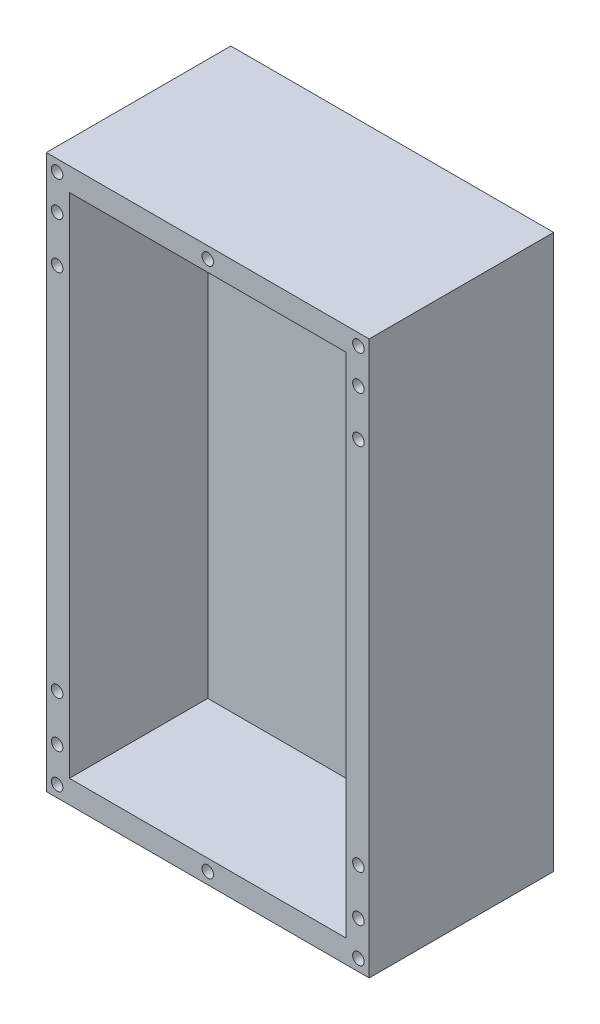
SolidWorks part; units mm, degrees
ref_plane "Front Plane" through (0, 0, 0) normal (0, 0, 1) x (1, 0, 0)
ref_plane "Top Plane" through (0, 0, 0) normal (0, 1, 0) x (1, 0, 0)
ref_plane "Right Plane" through (0, 0, 0) normal (1, 0, 0) x (0, 0, -1)
sketch "Sketch1" plane through (0, 0, 0) normal (0, 0, 1) x (1, 0, 0)
  line L0 (0, 609.6) -> (355.6, 0) construction
  line L1 (0, 609.6) -> (355.6, 609.6)
  line L2 (0, 609.6) -> (0, 0)
  line L3 (0, 0) -> (355.6, 0)
  line L4 (355.6, 609.6) -> (355.6, 0)
  line L5 (355.6, 609.6) -> (0, 0) construction
  line L9 (25.4, 584.2) -> (330.2, 584.2)
  line L10 (25.4, 584.2) -> (25.4, 25.4)
  line L11 (25.4, 25.4) -> (330.2, 25.4)
  line L12 (330.2, 584.2) -> (330.2, 25.4)
  line L13 (25.4, 584.2) -> (330.2, 25.4) construction
  line L14 (330.2, 584.2) -> (25.4, 25.4) construction
  point P12 (177.8, 304.8)
  point P13 (177.8, 304.8)
  dimension "D1" = 355.6
  dimension "D2" = 609.6
  dimension "D3" = 304.8
  dimension "D4" = 558.8
extrude "Boss-Extrude2" add sketch "Sketch1" along normal blind 203.2
ref_plane "Plane4" through (25.4, 584.2, 0) normal (0, -1, 0) x (-1, 0, 0)
sketch "Sketch4" plane through (0, 0, 0) normal (0, 0, -1) x (-1, 0, 0)
  line L1 (-330.2, 584.2) -> (-25.4, 584.2)
  line L2 (-330.2, 584.2) -> (-330.2, 25.4)
  line L3 (-330.2, 25.4) -> (-25.4, 25.4)
  line L4 (-25.4, 584.2) -> (-25.4, 25.4)
extrude "Boss-Extrude3" add sketch "Sketch4" against normal blind 50.8
sketch "Sketch5" plane through (0, 0, 203.2) normal (0, 0, 1) x (1, 0, 0)
  line L0 (177.8, 0) -> (177.8, 609.6) construction
  line L1 (0, 0) -> (355.6, 0) construction
  line L2 (355.6, 609.6) -> (0, 609.6) construction
  line L3 (355.6, 304.8) -> (0, 304.8) construction
  line L4 (355.6, 0) -> (355.6, 609.6) construction
  line L5 (0, 609.6) -> (0, 0) construction
  circle A0 centre (11.8857, 50.9474) radius 6.35
  circle A1 centre (11.8857, 101.7474) radius 6.35
  circle A2 centre (11.8857, 507.8526) radius 6.35
  circle A3 centre (11.8857, 558.6526) radius 6.35
  circle A4 centre (343.7143, 50.9474) radius 6.35
  circle A5 centre (343.7143, 101.7474) radius 6.35
  circle A6 centre (343.7143, 558.6526) radius 6.35
  circle A7 centre (343.7143, 507.8526) radius 6.35
  dimension "D1" = 12.7
  dimension "D2" = 50.8
extrude "Cut-Extrude1" cut sketch "Sketch5" against normal blind 25.4
sketch "Sketch6" plane through (0, 0, 203.2) normal (0, 0, 1) x (1, 0, 0)
  line L0 (0, 304.8) -> (355.6, 304.8) construction
  line L1 (0, 609.6) -> (0, 0) construction
  line L2 (355.6, 0) -> (355.6, 609.6) construction
  circle A0 centre (343.7143, 596.9) radius 6.35
  circle A1 centre (177.8, 596.9) radius 6.35
  circle A2 centre (11.8857, 596.9) radius 6.35
  circle A3 centre (343.7143, 12.7) radius 6.35
  circle A4 centre (177.8, 12.7) radius 6.35
  circle A5 centre (11.8857, 12.7) radius 6.35
extrude "Cut-Extrude2" cut sketch "Sketch6" against normal blind 12.7
sketch "Sketch8" plane through (0, 0, 50.8) normal (0, 0, 1) x (1, 0, 0)
  line L0 (60.1667, 127) -> (300.8333, 127) construction
